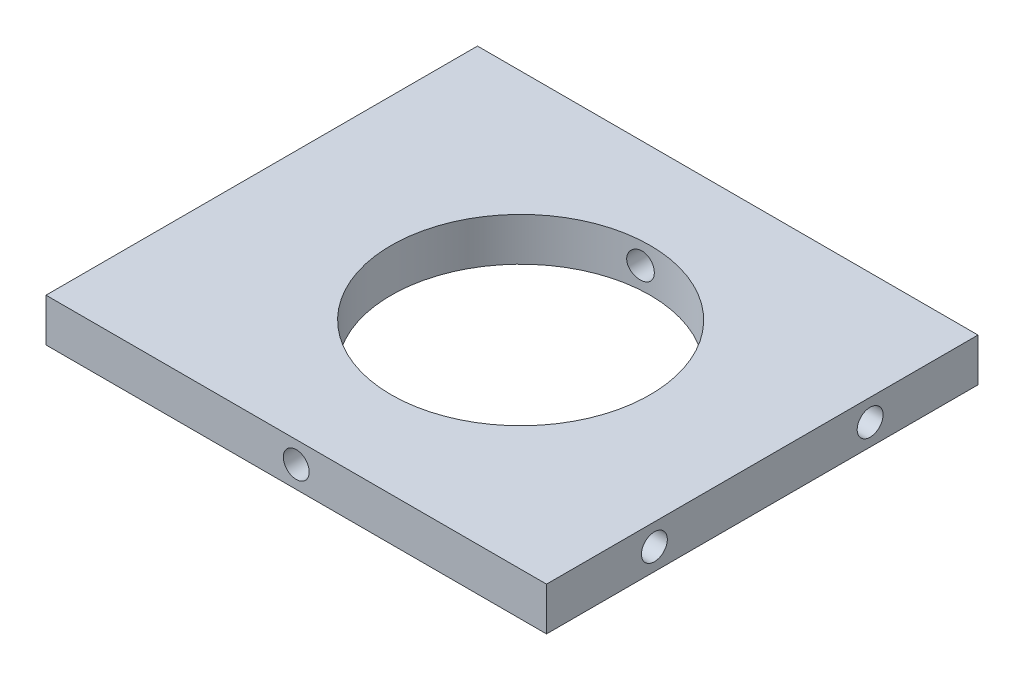
SolidWorks part; units mm, degrees
ref_plane "Plan de face" through (0, 0, 0) normal (0, 0, 1) x (1, 0, 0)
ref_plane "Plan de dessus" through (0, 0, 0) normal (0, 1, 0) x (1, 0, 0)
ref_plane "Plan de droite" through (0, 0, 0) normal (1, 0, 0) x (0, 0, -1)
sketch "Esquisse1" plane through (0, 0, 0) normal (0, 0, 1) x (1, 0, 0)
  line L0 (-5.5, -47.5) -> (52.5, -47.5) construction
  line L5 (-5.5, -45) -> (52.5, -45)
  line L6 (-5.5, -45) -> (-5.5, -50)
  line L7 (-5.5, -50) -> (52.5, -50)
  line L8 (52.5, -45) -> (52.5, -50)
  line L9 (23.5, -45) -> (23.5, -50) construction
  dimension "D1" = 5
  dimension "D2" = 58
extrude "Boss.-Extru.1" add sketch "Esquisse1" along normal blind 50
sketch "Esquisse2" plane through (0, -45, 0) normal (0, 1, 0) x (-1, 0, 0)
  line L0 (5.5, 50) -> (-52.5, 50) construction
  line L7 (-52.5, 50) -> (-52.5, 0) construction
  circle A0 centre (-24.5, 25) radius 15
  dimension "D10" = 28
  dimension "D11" = 25
extrude "Enlèv. mat.-Extru.1" cut sketch "Esquisse2" against normal through all
sketch "Esquisse3" plane through (-5.5, 0, 0) normal (-1, 0, 0) x (0, 0, 1)
  line L0 (50, -50) -> (0, -50) construction
  line L1 (0, -45) -> (0, -50) construction
  line L2 (50, -45) -> (50, -50) construction
  circle A0 centre (12.5, -47.5) radius 1.5
  circle A1 centre (37.5, -47.5) radius 1.5
  dimension "D1" = 2.5
  dimension "D2" = 2.5
  dimension "D3" = 12.5
  dimension "D4" = 12.5
extrude "Enlèv. mat.-Extru.2" cut sketch "Esquisse3" against normal blind 10
sketch "Esquisse4" plane through (52.5, 0, 0) normal (1, 0, 0) x (0, 0, -1)
  line L0 (-50, -50) -> (0, -50) construction
  line L1 (-50, -45) -> (-50, -50) construction
  line L2 (0, -45) -> (0, -50) construction
  circle A0 centre (-37.5, -47.5) radius 1.5
  circle A1 centre (-12.5, -47.5) radius 1.5
  dimension "D1" = 2.5
  dimension "D2" = 2.5
  dimension "D3" = 12.5
  dimension "D4" = 12.5
extrude "Enlèv. mat.-Extru.3" cut sketch "Esquisse4" against normal blind 10
sketch "Esquisse5" plane through (0, 0, 50) normal (0, 0, 1) x (1, 0, 0)
  line L0 (-5.5, -45) -> (-5.5, -50) construction
  line L1 (-5.5, -45) -> (52.5, -45) construction
  circle A0 centre (23.5, -47.5) radius 1.5
  dimension "D1" = 29
  dimension "D2" = 2.5
extrude "Enlèv. mat.-Extru.4" cut sketch "Esquisse5" against normal through all
